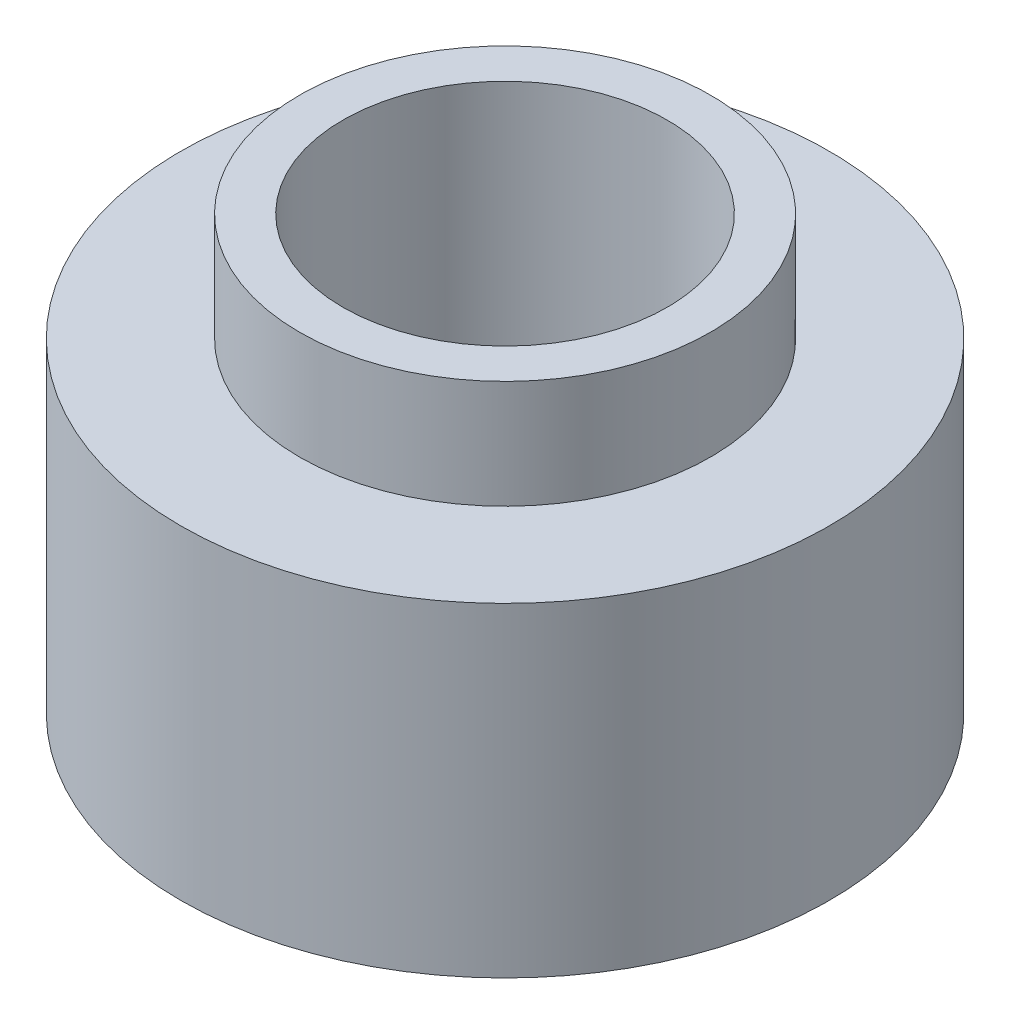
SolidWorks part; units mm, degrees
material "1023 Carbon Steel Sheet (SS)"
ref_plane "Front Plane" through (0, 0, 0) normal (0, 0, 1) x (1, 0, 0)
ref_plane "Top Plane" through (0, 0, 0) normal (0, 1, 0) x (1, 0, 0)
ref_plane "Right Plane" through (0, 0, 0) normal (1, 0, 0) x (0, 0, -1)
sketch "Sketch1" plane through (0, 0, 0) normal (0, 0, 1) x (1, 0, 0)
  line L0 (0, 9.2385) -> (0, -9.7406) construction
  line L1 (4.7625, 0) -> (4.7625, 12.7)
  line L2 (4.7625, 12.7) -> (6.0325, 12.7)
  line L3 (6.0325, 12.7) -> (6.0325, 9.525)
  line L4 (6.0325, 9.525) -> (9.525, 9.525)
  line L5 (9.525, 9.525) -> (9.525, 0)
  line L6 (9.525, 0) -> (4.7625, 0)
  dimension "D1" = 3.175
  dimension "D2" = 9.525
  dimension "D3" = 1.27
  dimension "D4" = 4.7625
  dimension "D5" = 4.7625
  dimension "D6" = 0
revolve "Revolve1" add sketch "Sketch1" angle 360 about L0
